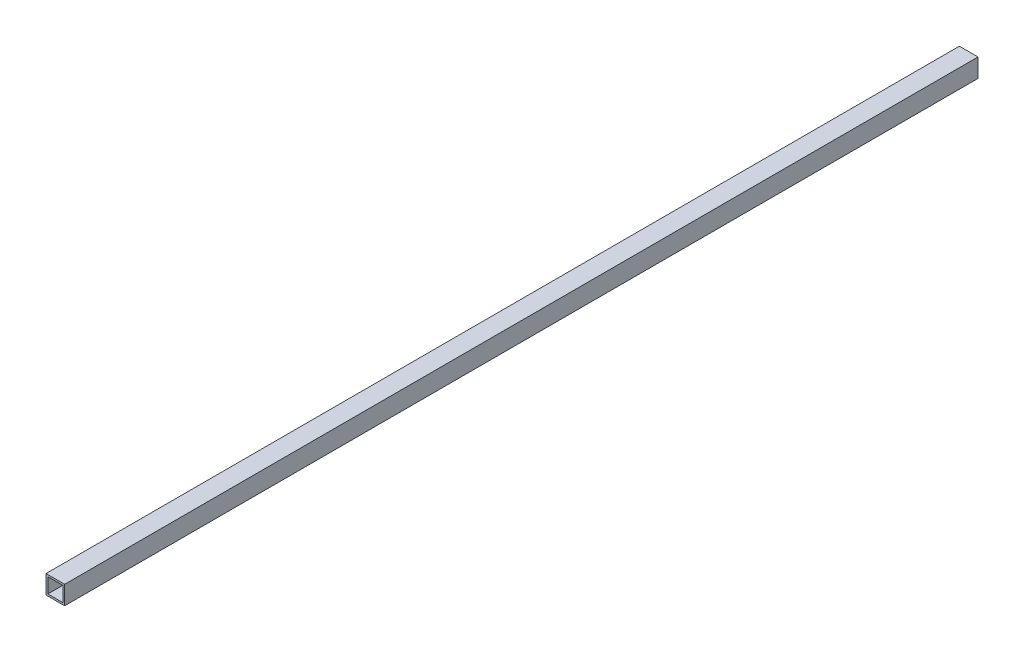
SolidWorks part; units mm, degrees
material "1.0037 (S235JR)"
ref_plane "Front Plane" through (0, 0, 0) normal (0, 0, 1) x (1, 0, 0)
ref_plane "Top Plane" through (0, 0, 0) normal (0, 1, 0) x (1, 0, 0)
ref_plane "Right Plane" through (0, 0, 0) normal (1, 0, 0) x (0, 0, -1)
curve "Curve1"
  spline degree 1 poles (0, 0, 0) (0, 0, 1960) knots 0 0 1 1
sketch "Sketch1" plane through (0, 0, 0) normal (0, 0, 1) x (1, 0, 0)
  line L0 (0, 35.3535) -> (0, -33.8384) construction
  line L1 (-20, 20) -> (20, 20)
  line L2 (-20, 20) -> (-20, -20)
  line L3 (-20, -20) -> (20, -20)
  line L4 (20, 20) -> (20, -20)
  line L5 (-16, 16) -> (16, 16)
  line L6 (-16, 16) -> (-16, -16)
  line L7 (-16, -16) -> (16, -16)
  line L8 (16, 16) -> (16, -16)
  line L9 (-39.3939, 0) -> (41.5152, 0) construction
  dimension "D1" = 40
  dimension "D2" = 32
sweep "Sweep1" add profiles "Sketch1" path "Curve1"
